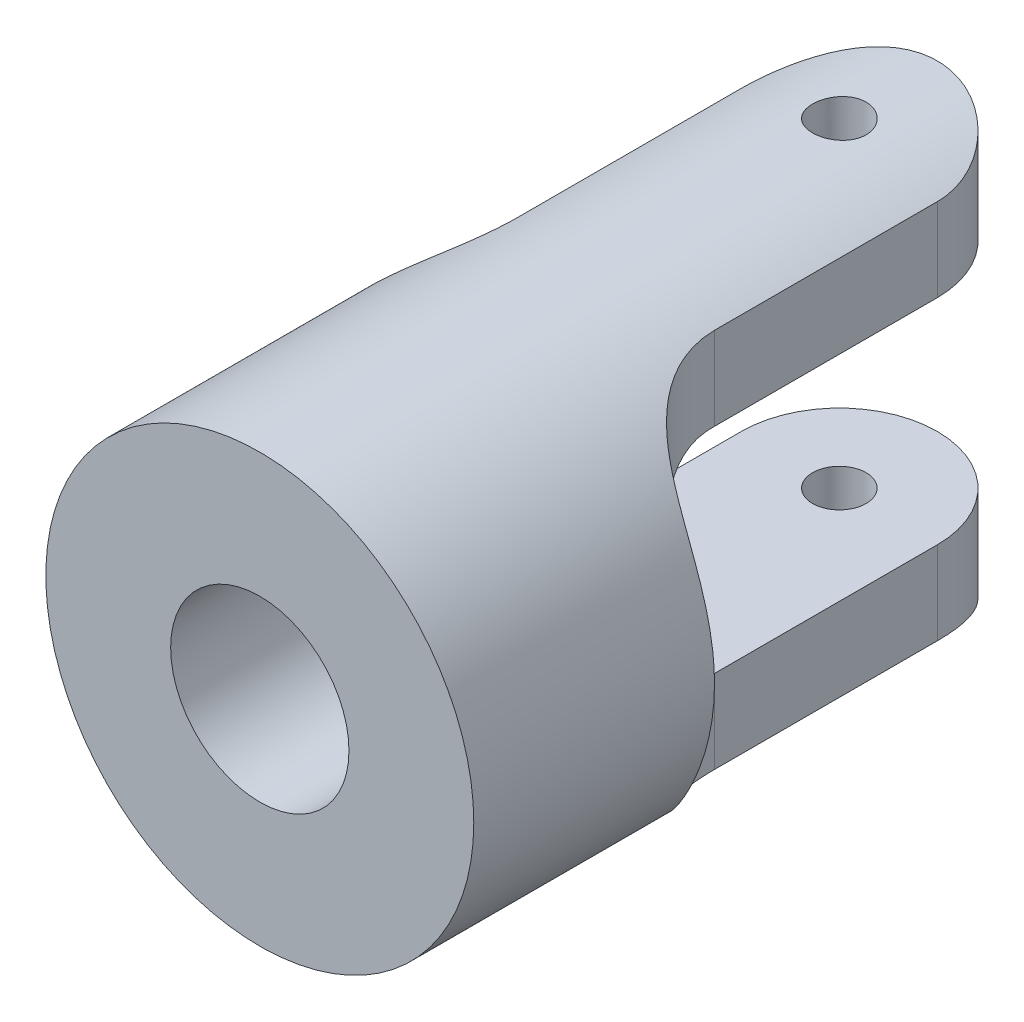
SolidWorks part; units mm, degrees
ref_plane "前视基准面" through (0, 0, 0) normal (0, 0, 1) x (1, 0, 0)
ref_plane "上视基准面" through (0, 0, 0) normal (0, 1, 0) x (1, 0, 0)
ref_plane "右视基准面" through (0, 0, 0) normal (1, 0, 0) x (0, 0, -1)
sketch "草图1" plane through (0, 0, 0) normal (0, 0, 1) x (1, 0, 0)
  circle A0 centre (0, 0) radius 6
  circle A1 centre (0, 0) radius 2.5
  dimension "D1" = 12
  dimension "D2" = 5
extrude "凸台-拉伸1" add sketch "草图1" along normal blind 19
sketch "草图2" plane through (0, 0, 0) normal (0, 1, 0) x (1, 0, 0)
  line L0 (0, 3.1848) -> (0, -21.7389) construction
  line L1 (-11.4446, -9) -> (14.3905, -9) construction
  line L2 (-2.75, -2.75) -> (-2.75, -9)
  line L4 (-6, 0) -> (-6, -19) construction
  line L5 (-6, -19) -> (6, -19) construction
  line L6 (-6, -2.0062) -> (-6, -15.979) construction
  line L7 (-6, -12.25) -> (-6, -19)
  line L8 (-6, -19) -> (6, -19)
  line L9 (6, -12.25) -> (6, -19)
  line L10 (2.75, -2.75) -> (2.75, -9)
  arc A0 (2.75, -2.75) -> (-2.75, -2.75) centre (0, -2.75) ccw
  arc A2 (-6, -12.25) -> (-2.75, -9) centre (-6, -9) ccw
  arc A3 (6, -12.25) -> (2.75, -9) centre (6, -9) cw
  circle A4 centre (0, -2.75) radius 0.75
  dimension "D1" = 5.5
  dimension "D2" = 10
  dimension "D3" = 1.5
extrude "切除-拉伸1" cut sketch "草图2" against normal mid plane 19 flip side to cut
sketch "草图3" plane through (0, 0, 0) normal (1, 0, 0) x (0, 0, -1)
  line L0 (-21.1395, 0) -> (4.4517, 0) construction
  line L1 (-9.25, 3) -> (0, 3)
  line L2 (0, 2.5) -> (0, 6) construction
  line L3 (0, 3) -> (0, -3)
  line L4 (0, -6) -> (0, -2.4999) construction
  line L5 (0, -3) -> (-9.25, -3)
  arc A0 (-9.25, 3) -> (-9.25, -3) centre (-9.25, 0) ccw
  spline S1 degree 3 poles (-9, 5.3327) (-9.3489, 5.3327) (-9.6897, 5.3051) (-10.1779, 5.2159) (-10.3329, 5.1787) (-10.6283, 5.0872) (-10.7698, 5.0323) (-11.0313, 4.9047) (-11.1508, 4.8325) (-11.3691, 4.6696) (-11.4686, 4.5779) (-11.6436, 4.3792) (-11.7196, 4.2721) (-11.8523, 4.0422) (-11.9093, 3.9185) (-12.0526, 3.5326) (-12.1137, 3.2543) (-12.1762, 2.8069) (-12.192, 2.6524) (-12.2163, 2.34) (-12.2248, 2.1814) (-12.2435, 1.6983) (-12.2472, 1.3667) (-12.2504, 0.6843) (-12.25, 0.3412) (-12.25, -0.3433) (-12.2504, -0.687) (-12.2472, -1.3688) (-12.2435, -1.6999) (-12.2185, -2.3429) (-12.1972, -2.6566) (-12.1136, -3.2548) (-12.0524, -3.5333) (-11.9091, -3.9189) (-11.8521, -4.0427) (-11.7194, -4.2724) (-11.6436, -4.3792) (-11.4694, -4.577) (-11.3699, -4.6689) (-11.1511, -4.8323) (-11.032, -4.9042) (-10.7735, -5.0307) (-10.6328, -5.0857) (-10.3348, -5.1783) (-10.1798, -5.2154) (-9.8578, -5.2745) (-9.6895, -5.2965) (-9.3474, -5.3255) (-9.1746, -5.3327) (-9, -5.3327) knots 0 0 0 0 0.0625 0.0625 0.09375 0.09375 0.125 0.125 0.15625 0.15625 0.1875 0.1875 0.21875 0.21875 0.25 0.25 0.3125 0.3125 0.34375 0.34375 0.375 0.375 0.4375 0.4375 0.5 0.5 0.5625 0.5625 0.625 0.625 0.6875 0.6875 0.75 0.75 0.78125 0.78125 0.8125 0.8125 0.84375 0.84375 0.875 0.875 0.90625 0.90625 0.9375 0.9375 0.96875 0.96875 1 1 1 1 construction
  dimension "D1" = 6
extrude "切除-拉伸2" cut sketch "草图3" against normal mid plane 19
